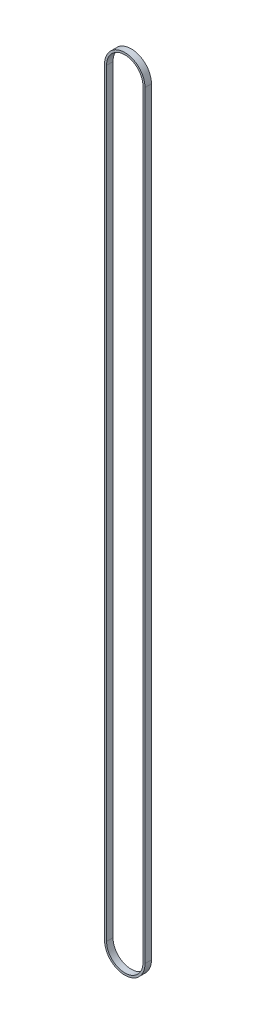
SolidWorks part; units mm, degrees
ref_plane "Front Plane" through (0, 0, 0) normal (0, 0, 1) x (1, 0, 0)
ref_plane "Top Plane" through (0, 0, 0) normal (0, 1, 0) x (1, 0, 0)
ref_plane "Right Plane" through (0, 0, 0) normal (1, 0, 0) x (0, 0, -1)
sketch "Sketch1" plane through (0, 0, 0) normal (0, 0, 1) x (1, 0, 0)
  line L0 (-10, 0) -> (-10, 375)
  line L2 (10, 375) -> (10, 0)
  circle A0 centre (0, 0) radius 10 construction
  circle A1 centre (0, 375) radius 10 construction
  arc A2 (-10, 375) -> (10, 375) centre (0, 375) cw
  arc A3 (10, 0) -> (-10, 0) centre (0, 0) cw
  point P8 (0, 103.5831)
  point P10 (0, 148.9234)
  point P11 (0, 71.2876)
  point P12 (0, 233.4417)
  dimension "D1" = 20
  dimension "D2" = 375
extrude "Extrude-Thin1" add sketch "Sketch1" along normal blind 3.175 thin
